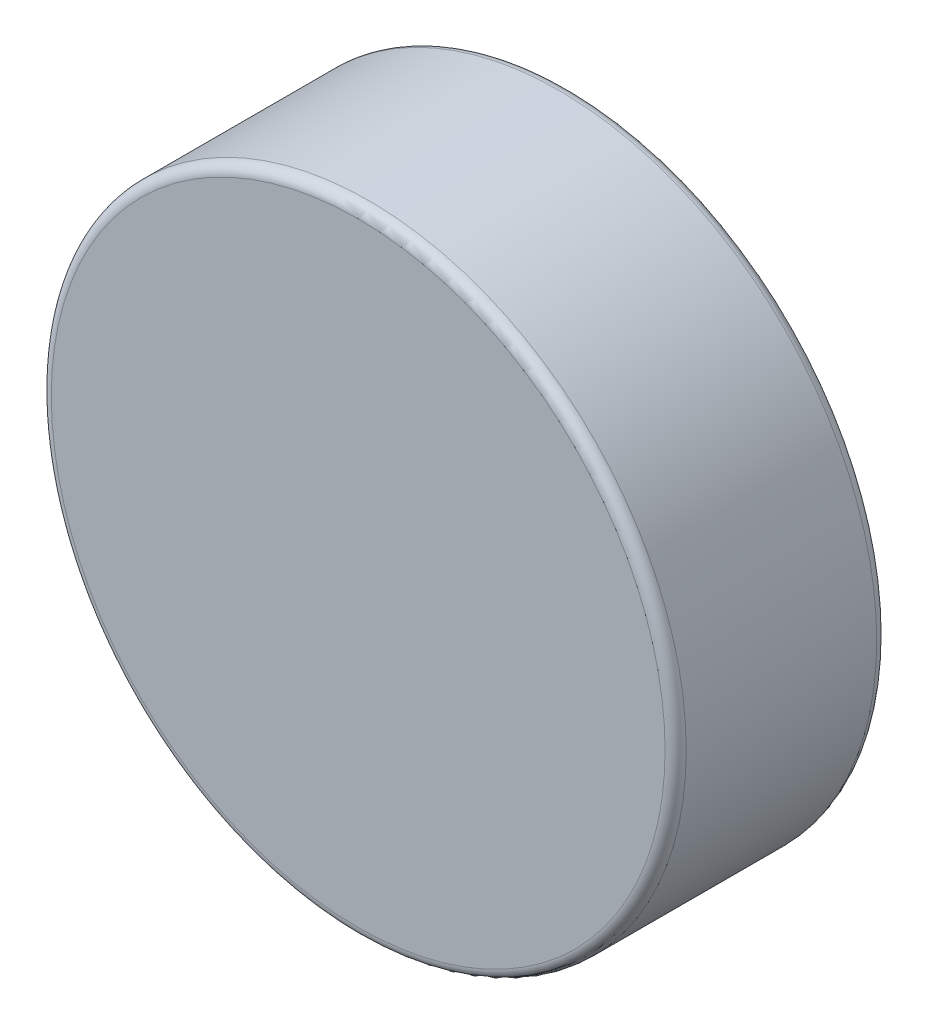
SolidWorks part; units mm, degrees
material "Nickel"
ref_plane "Front Plane" through (0, 0, 0) normal (0, 0, 1) x (1, 0, 0)
ref_plane "Top Plane" through (0, 0, 0) normal (0, 1, 0) x (1, 0, 0)
ref_plane "Right Plane" through (0, 0, 0) normal (1, 0, 0) x (0, 0, -1)
sketch "Sketch1" plane through (0, 0, 0) normal (0, 0, 1) x (1, 0, 0)
  circle A0 centre (0, 0) radius 38.1
  dimension "D1" = 76.2
extrude "Boss-Extrude1" add sketch "Sketch1" along normal blind 25.4
fillet "Fillet1" radius 1.27 2 edges at (38.1, 0, 0) (38.1, 0, 25.4)
